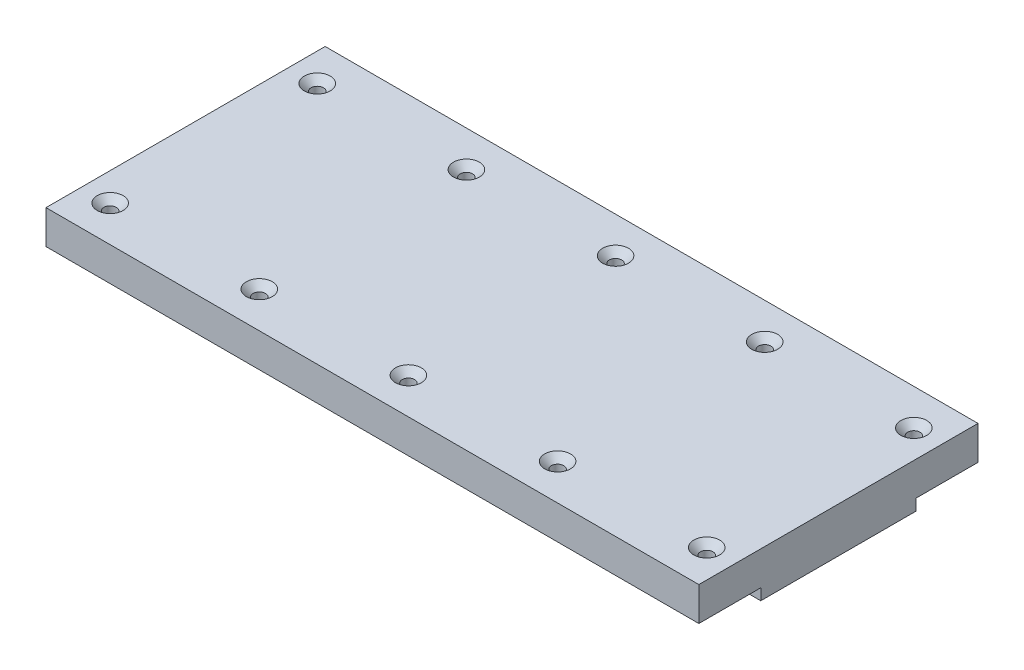
SolidWorks part; units mm, degrees
ref_plane "Alzado" through (0, 0, 0) normal (0, 0, 1) x (1, 0, 0)
ref_plane "Planta" through (0, 0, 0) normal (0, 1, 0) x (1, 0, 0)
ref_plane "Vista lateral" through (0, 0, 0) normal (1, 0, 0) x (0, 0, -1)
sketch "Croquis2" plane through (0, 0, 0) normal (1, 0, 0) x (0, 0, -1)
  line L0 (-69, -10) -> (69, -10)
  line L1 (69, -10) -> (69, 0)
  line L2 (69, 0) -> (124, 0)
  line L3 (124, 0) -> (124, 30)
  line L4 (124, 30) -> (-124, 30)
  line L5 (-124, 30) -> (-124, 0)
  line L6 (-124, 0) -> (-69, 0)
  line L7 (-69, 0) -> (-69, -10)
  point P3 (0, -10)
  point P10 (0, 0)
  point P11 (0, 0)
  point P12 (35.84, 0)
  point P13 (0, 30)
  point P14 (0, 0)
  dimension "D1" = 40
  dimension "D2" = 138
  dimension "D3" = 10
  dimension "D4" = 248
extrude "Saliente-Extruir1" add sketch "Croquis2" against normal blind 580
sketch "Croquis3" plane through (0, 30, 0) normal (0, 1, 0) x (1, 0, 0)
  line L0 (0, 0) -> (-580, 0) construction
  line L1 (0, 124) -> (0, -124) construction
  line L2 (-555, 92) -> (-555, -92) construction
  line L3 (-580, 124) -> (-580, -124) construction
  circle A0 centre (-555, 92) radius 5.5
  circle A1 centre (-555, -92) radius 5.5
  circle A2 centre (-422.5, 92) radius 5.5
  circle A3 centre (-422.5, -92) radius 5.5
  circle A4 centre (-290, 92) radius 5.5
  circle A5 centre (-290, -92) radius 5.5
  circle A6 centre (-157.5, 92) radius 5.5
  circle A7 centre (-157.5, -92) radius 5.5
  circle A8 centre (-25, 92) radius 5.5
  circle A9 centre (-25, -92) radius 5.5
  point P8 (-555, 0)
  dimension "D3" = 11
  dimension "D1" = 184
  dimension "D2" = 25
  dimension "D5" = 25
  dimension "D4" = 5
extrude "Cortar-Extruir1" cut sketch "Croquis3" against normal up to next
chamfer "Chaflán1" distance 6 angle 45 10 edges at (-25, 30, 97.5) (-25, 30, -86.5) (-157.5, 30, -86.5) (-157.5, 30, 97.5) (-290, 30, -86.5) (-290, 30, 97.5) (-422.5, 30, -86.5) (-555, 30, -86.5) (-555, 30, 97.5) (-422.5, 30, 97.5)
